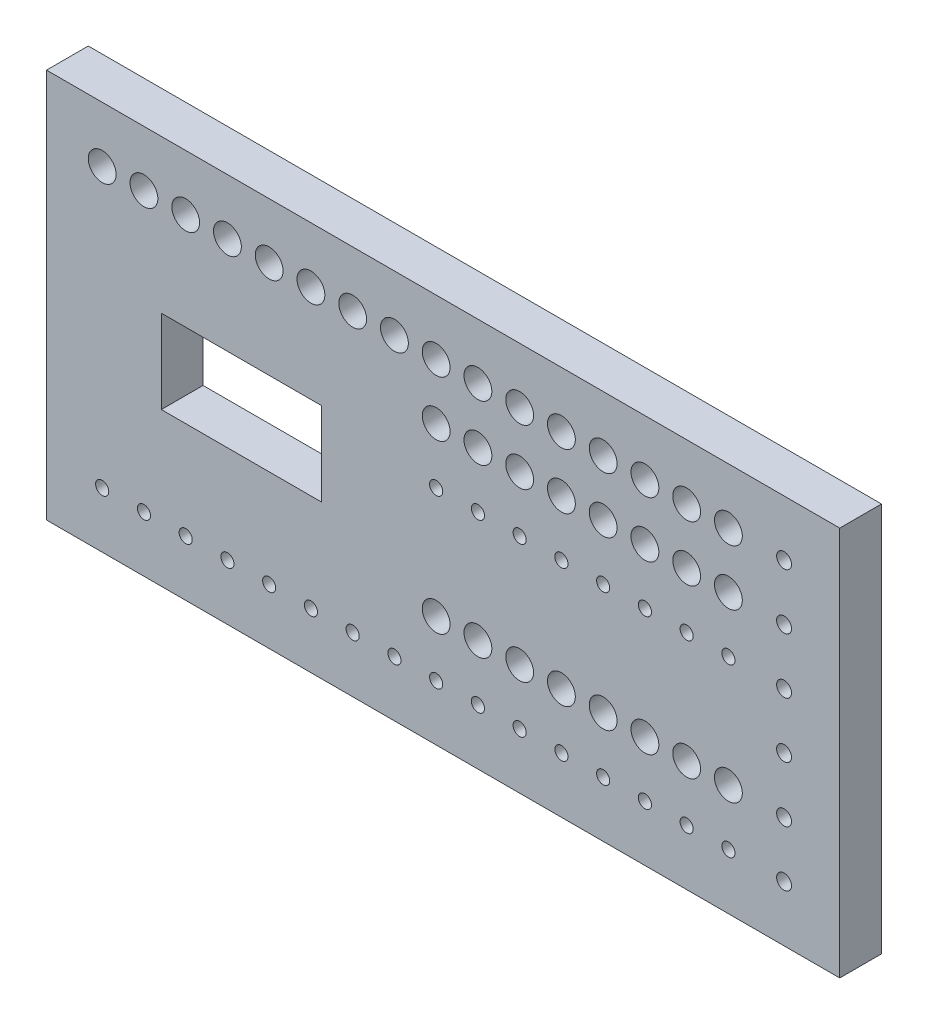
SolidWorks part; units mm, degrees
material "Oak"
ref_plane "Front Plane" through (0, 0, 0) normal (0, 0, 1) x (1, 0, 0)
ref_plane "Top Plane" through (0, 0, 0) normal (0, 1, 0) x (1, 0, 0)
ref_plane "Right Plane" through (0, 0, 0) normal (1, 0, 0) x (0, 0, -1)
sketch "Sketch1" plane through (0, 0, 0) normal (0, 0, 1) x (1, 0, 0)
  line L0 (261.9375, 51.9209) -> (261.9375, -81.889) construction
  line L6 (-22.225, -30.6291) -> (50.8, -30.6291)
  line L7 (-22.225, -30.6291) -> (-22.225, 7.4709)
  line L8 (-74.6125, 77.3209) -> (287.3375, 77.3209)
  line L9 (-74.6125, 77.3209) -> (-74.6125, -100.4791)
  line L10 (-74.6125, -100.4791) -> (287.3375, -100.4791)
  line L11 (287.3375, 77.3209) -> (287.3375, -100.4791)
  line L12 (-22.225, 7.4709) -> (50.8, 7.4709)
  line L13 (50.8, -30.6291) -> (50.8, 7.4709)
  line L18 (103.1875, 7.4709) -> (103.1875, -5.2291) construction
  line L19 (99.7585, 1.1209) -> (106.6165, 1.1209) construction
  line L20 (14.2875, 7.4709) -> (14.2875, -30.6291) construction
  line L21 (-22.225, -11.5791) -> (50.8, -11.5791) construction
  circle A0 centre (-49.2125, 51.9209) radius 6.35
  circle A1 centre (-30.1625, 51.9209) radius 6.35
  circle A2 centre (-11.1125, 51.9209) radius 6.35
  circle A3 centre (7.9375, 51.9209) radius 6.35
  circle A4 centre (26.9875, 51.9209) radius 6.35
  circle A5 centre (46.0375, 51.9209) radius 6.35
  circle A6 centre (65.0875, 51.9209) radius 6.35
  circle A7 centre (84.1375, 51.9209) radius 6.35
  circle A8 centre (103.1875, 51.9209) radius 6.35
  circle A9 centre (122.2375, 51.9209) radius 6.35
  circle A10 centre (141.2875, 51.9209) radius 6.35
  circle A11 centre (160.3375, 51.9209) radius 6.35
  circle A12 centre (179.3875, 51.9209) radius 6.35
  circle A13 centre (198.4375, 51.9209) radius 6.35
  circle A14 centre (217.4875, 51.9209) radius 6.35
  circle A15 centre (236.5375, 51.9209) radius 6.35
  circle A16 centre (103.1875, 26.5209) radius 6.35
  circle A17 centre (122.2375, 26.5209) radius 6.35
  circle A18 centre (141.2875, 26.5209) radius 6.35
  circle A19 centre (160.3375, 26.5209) radius 6.35
  circle A20 centre (179.3875, 26.5209) radius 6.35
  circle A21 centre (198.4375, 26.5209) radius 6.35
  circle A22 centre (217.4875, 26.5209) radius 6.35
  circle A23 centre (236.5375, 26.5209) radius 6.35
  circle A24 centre (103.1875, -49.6791) radius 6.35
  circle A25 centre (122.2375, -49.6791) radius 6.35
  circle A26 centre (141.2875, -49.6791) radius 6.35
  circle A27 centre (160.3375, -49.6791) radius 6.35
  circle A28 centre (179.3875, -49.6791) radius 6.35
  circle A29 centre (198.4375, -49.6791) radius 6.35
  circle A30 centre (217.4875, -49.6791) radius 6.35
  circle A31 centre (236.5375, -49.6791) radius 6.35
  circle A32 centre (103.1875, 1.1209) radius 3
  circle A33 centre (122.2375, 1.1209) radius 3
  circle A34 centre (141.2875, 1.1209) radius 3
  circle A35 centre (160.3375, 1.1209) radius 3
  circle A36 centre (179.3875, 1.1209) radius 3
  circle A37 centre (198.4375, 1.1209) radius 3
  circle A38 centre (217.4875, 1.1209) radius 3
  circle A39 centre (236.5375, 1.1209) radius 3
  circle A40 centre (-49.2125, -75.0791) radius 3
  circle A41 centre (-30.1625, -75.0791) radius 3
  circle A42 centre (-11.1125, -75.0791) radius 3
  circle A43 centre (7.9375, -75.0791) radius 3
  circle A44 centre (26.9875, -75.0791) radius 3
  circle A45 centre (46.0375, -75.0791) radius 3
  circle A46 centre (65.0875, -75.0791) radius 3
  circle A47 centre (84.1375, -75.0791) radius 3
  circle A48 centre (103.1875, -75.0791) radius 3
  circle A49 centre (122.2375, -75.0791) radius 3
  circle A50 centre (141.2875, -75.0791) radius 3
  circle A51 centre (160.3375, -75.0791) radius 3
  circle A52 centre (179.3875, -75.0791) radius 3
  circle A53 centre (198.4375, -75.0791) radius 3
  circle A54 centre (217.4875, -75.0791) radius 3
  circle A55 centre (236.5375, -75.0791) radius 3
  circle A56 centre (261.9375, 51.9209) radius 3.4
  circle A57 centre (261.9375, 26.5209) radius 3.4
  circle A58 centre (261.9375, -24.2791) radius 3.4
  circle A59 centre (261.9375, -75.0791) radius 3.4
  circle A60 centre (261.9375, -49.6791) radius 3.4
  circle A61 centre (261.9375, 1.1209) radius 3.4
  point P0 (14.2875, -11.5791)
  dimension "D3" = 12.7
  dimension "D4" = 73.025
  dimension "D6" = 19.05
  dimension "D7" = 12.7
  dimension "D8" = 25.4
  dimension "D10" = 19.05
  dimension "D11" = 12.7
  dimension "D14" = 19.05
  dimension "D15" = 6
  dimension "D18" = 19.05
  dimension "D19" = 6
  dimension "D20" = 25.4
  dimension "D22" = 6.8
  dimension "D23" = 25.4
  dimension "D24" = 25.4
  dimension "D25" = 25.4
  dimension "D26" = 25.4
  dimension "D27" = 25.4
  dimension "D30" = 25.4
  dimension "D12" = 76.2
  dimension "D16" = 25.4
  dimension "D21" = 19.05
  dimension "D28" = 25.4
  dimension "D29" = 38.1
  dimension "D31" = 25.4
  dimension "D32" = 25.4
  dimension "D33" = 88.9
  dimension "D34" = 88.9
  dimension "D35" = 361.95
  dimension "D36" = 16
  dimension "D5" = 16
  dimension "D9" = 8
  dimension "D13" = 8
  dimension "D17" = 8
extrude "Boss-Extrude1" add sketch "Sketch1" along normal blind 19.05 contours L11 L8 L9 L10 A61 A60 A59 A58 A57 A56 A55 A54 A53 A52 A51 A50 A49 A48 A47 A46 A45 A44 A43 A42 A41 A40 A39
